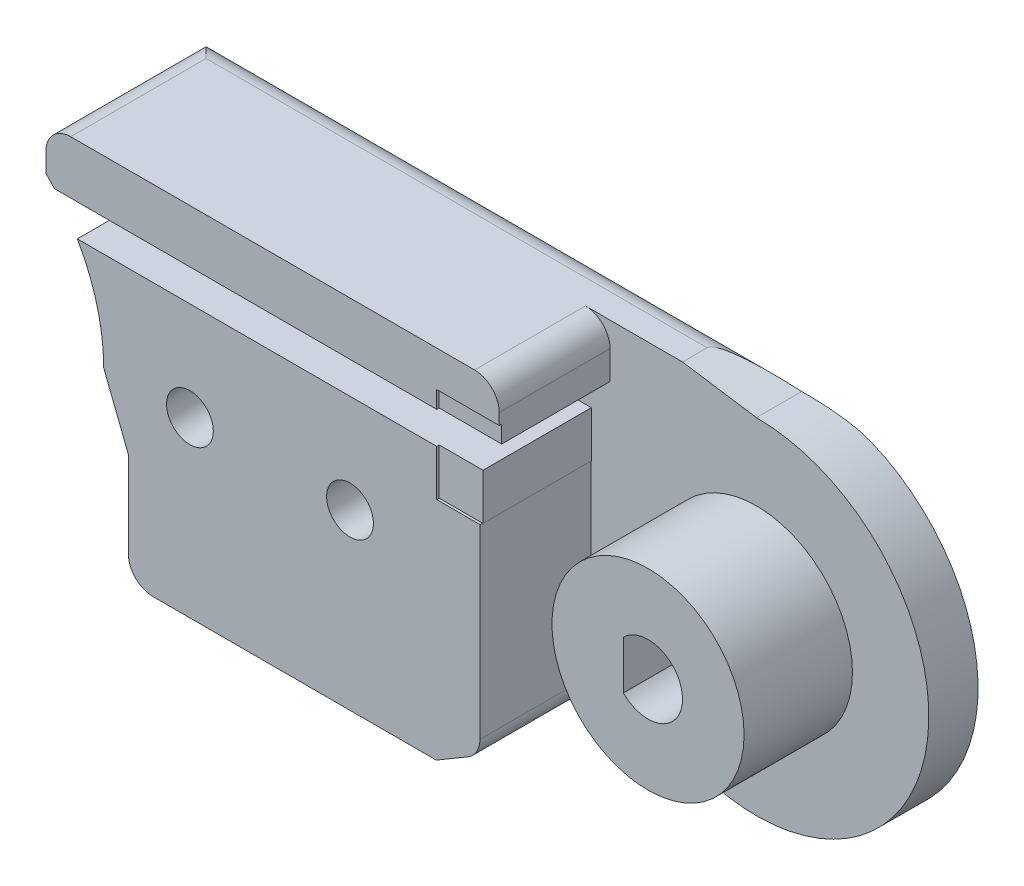
SolidWorks part; units mm, degrees
ref_plane "Front Plane" through (0, 0, 0) normal (0, 0, 1) x (1, 0, 0)
ref_plane "Top Plane" through (0, 0, 0) normal (0, 1, 0) x (1, 0, 0)
ref_plane "Right Plane" through (0, 0, 0) normal (1, 0, 0) x (0, 0, -1)
sketch "Sketch3" plane through (0, 0, 0) normal (0, 0, 1) x (1, 0, 0)
  line L7 (8, 0) -> (9, -2.5431)
  line L11 (30, 7) -> (27, 7.4569)
  line L13 (0, 7) -> (0, 7.5) construction
  line L14 (0, 7.5) -> (-22.3287, 7.5) construction
  line L15 (0, 5.3) -> (-14, 5.3) construction
  line L16 (0, 4) -> (-14, 4) construction
  line L17 (-14, 4) -> (-14, 5.3) construction
  line L18 (5.6569, 5.6569) -> (5.6569, 7.4569)
  line L19 (5.6569, 7.4569) -> (27, 7.4569)
  line L20 (21.5, -7.0431) -> (9, -7.0431)
  line L21 (9, -7.0431) -> (9, -2.5431)
  line L23 (25.0503, -4.9497) -> (21.5, -7.0431)
  arc A4 (8, 0) -> (5.6569, 5.6569) centre (0, 0) ccw
  arc A5 (25.0503, -4.9497) -> (30, 7) centre (30, 0) ccw
  circle A6 centre (0, 0) radius 7 construction
  circle A7 centre (0, 0) radius 3.9 construction
  circle A8 centre (0, 0) radius 5.3 construction
  circle A9 centre (0, 0) radius 4 construction
  dimension "D3" = 3.5503
  dimension "D17" = 14
  dimension "D4" = 14.5
  dimension "D5" = 135
  dimension "D2" = 5.6569
  dimension "D6" = 12.5
  dimension "D7" = 4.5
  dimension "D8" = 1
  dimension "D9" = 45
  dimension "D11" = 1.8
  dimension "D12" = 30
  dimension "D14" = 3
extrude "Boss-Extrude1" add sketch "Sketch3" along normal blind 2 contours A5 L11 L19 L18 A4 L7 L21 L20 L23
sketch "Sketch20" plane through (0, 0, 0) normal (0, 0, 1) x (1, 0, 0)
  line L0 (0, 7) -> (0, 7.5) construction
  line L1 (0, 7.5) -> (-19.4737, 7.5) construction
  line L2 (0, 5.3) -> (-14, 5.3) construction
  line L3 (0, 4) -> (-14, 4) construction
  line L4 (-14, 4) -> (-14, 5.3) construction
  line L5 (0, 5.3) -> (17.4849, 5.3) construction
  line L6 (17.4849, 5.3) -> (17.4849, 4) construction
  line L7 (17.4849, 4) -> (0, 4) construction
  line L8 (-2.5, 7.5) -> (-2.5, 2.868) construction
  circle A0 centre (0, 0) radius 7 construction
  circle A1 centre (0, 0) radius 3.9 construction
  circle A3 centre (0, 0) radius 5.3 construction
  circle A4 centre (0, 0) radius 4 construction
  circle A5 centre (0, 0) radius 2 construction
  dimension "D1" = 0
  dimension "D2" = 2.5
ref_plane "Plane1" through (0, 0, 2) normal (0, 0, 1) x (1, 0, 0)
sketch "Sketch4" plane through (0, 0, 2) normal (0, 0, 1) x (1, 0, 0)
  line L4 (5.6569, 5.6569) -> (5.6569, 7.5)
  line L5 (5.6569, 5.6569) -> (5.6569, 7.4569) construction
  line L6 (5.6569, 7.5) -> (21.5, 7.5)
  line L10 (8, 0) -> (9, -2.5431)
  line L11 (9, -2.5431) -> (9, -7.0431)
  line L12 (9, -7.0431) -> (21.5, -7.0431)
  line L13 (21.5, -7.0431) -> (21.5, 7.5)
  arc A0 (8, 0) -> (5.6569, 5.6569) centre (0, 0) ccw construction
  arc A3 (8, 0) -> (5.6569, 5.6569) centre (0, 0) ccw
sketch "Sketch22" plane through (0, 0, 2) normal (0, 0, 1) x (1, 0, 0)
  line L1 (5.6569, 7.4569) -> (21.5, 7.4569)
  line L6 (8, 0) -> (9, -2.5431)
  line L7 (9, -2.5431) -> (9, -7.0431)
  line L8 (9, -7.0431) -> (21.5, -7.0431)
  line L10 (21.5, 7.4569) -> (27, 7.4569)
  line L11 (27, 7.4569) -> (27, 2.1289)
  line L12 (27, 2.1289) -> (23.2751, 2.1289)
  line L13 (21.5, -7.0431) -> (23.2751, -5.9964)
  line L14 (25.0503, -4.9497) -> (21.5, -7.0431) construction
  line L15 (23.2751, -5.9964) -> (23.2751, 2.1289)
  line L16 (5.6569, 7.4569) -> (5.6569, 5.6569)
  arc A0 (8, 0) -> (5.6569, 5.6569) centre (0, 0) ccw
  dimension "D1" = 5.328
extrude "Boss-Extrude6" add sketch "Sketch22" along normal blind 4.5
sketch "Sketch25" plane through (0, 0, 2) normal (0, 0, 1) x (1, 0, 0)
  line L0 (0, 5.3) -> (18.0981, 5.3) construction
  line L1 (0, 4) -> (18.0981, 4) construction
  line L2 (18.0981, 4) -> (18.0981, 5.3) construction
sketch "Sketch26" plane through (0, 0, 2) normal (0, 0, 1) x (1, 0, 0)
  line L1 (18.0981, 5.3) -> (2.5301, 5.3)
  line L2 (18.0981, 4) -> (2.5301, 4)
  line L3 (2.5301, 5.3) -> (2.5301, 4)
  line L4 (18.0981, 5.3) -> (27, 5.3)
  line L5 (27, 2.1289) -> (27, 7.4569) construction
  line L6 (27, 5.3) -> (27, 4)
  line L7 (27, 4) -> (18.0981, 4)
extrude "Cut-Extrude6" cut sketch "Sketch26" along normal blind 4.5
ref_plane "Plane18" through (0, 0, 6.5) normal (0, 0, 1) x (1, 0, 0)
sketch "Sketch31" plane through (0, 0, 6.5) normal (0, 0, 1) x (1, 0, 0)
  line L0 (2.4327, 5.6569) -> (0, 5.6569)
  line L4 (9, -5.6569) -> (0, -5.6569)
  line L7 (2.4327, 5.6569) -> (5.6569, 5.6569)
  line L8 (5.6569, 5.6569) -> (5.6569, 7.4569)
  line L12 (9, -7.0431) -> (9, -5.6569)
  line L13 (9, -2.5431) -> (9, -7.0431) construction
  line L16 (27, 7.4569) -> (27, 2.1289)
  line L17 (27, 2.1289) -> (23.2751, 2.1289)
  line L18 (23.2751, -5.9964) -> (23.2751, 2.1289)
  line L21 (21.5, -7.0431) -> (23.2751, -5.9964)
  line L22 (5.6569, 7.4569) -> (5.6569, 8.9569)
  line L23 (5.6569, 8.9569) -> (27, 8.9569)
  line L24 (27, 8.9569) -> (27, 7.4569)
  line L25 (9, -7.0431) -> (9, -8.5431)
  line L26 (9, -8.5431) -> (21.5, -8.5431)
  line L27 (21.5, -8.5431) -> (21.5, -7.0431)
  line L28 (27, 7.4569) -> (5.6569, 7.4569) construction
  line L29 (9, -7.0431) -> (21.5, -7.0431) construction
  arc A0 (0, 5.6569) -> (0, -5.6569) centre (0, 0) ccw
  dimension "D1" = 5.6569
  dimension "D2" = 5.6569
  dimension "D3" = 1.5
  dimension "D4" = 1.5
extrude "Boss-Extrude14" add sketch "Sketch31" along normal blind 2.3 separate body
sketch "Sketch32" plane through (0, 0, 8.8) normal (0, 0, 1) x (1, 0, 0)
  circle A0 centre (0, 0) radius 3
  dimension "D1" = 6
extrude "Cut-Extrude7" cut sketch "Sketch32" against normal blind 2.3
sketch "Sketch33" plane through (0, 0, 8.8) normal (0, 0, 1) x (1, 0, 0)
  line L1 (5.6569, 8.9569) -> (5.6569, 6.9569)
  line L4 (9, -7.0431) -> (9, -8.5431)
  line L7 (7, -4.1569) -> (23.2751, -4.1569)
  line L11 (9, -8.5431) -> (21.5, -8.5431)
  line L15 (21.5, -8.5431) -> (21.5, -7.0431)
  line L16 (21.5, -7.0431) -> (9, -7.0431)
  line L17 (5.6569, 8.9569) -> (23, 8.9569)
  line L18 (27, 8.9569) -> (5.6569, 8.9569) construction
  line L21 (23, 6.9569) -> (23, 8.9569)
  line L22 (23.2751, -4.1569) -> (23.2751, -2.1569)
  line L23 (23.2751, -2.1569) -> (7, -2.1569)
  line L25 (23.2751, -5.9964) -> (23.2751, 2.1289) construction
  line L27 (5.6569, 6.9569) -> (23, 6.9569)
  line L28 (19, 2.172) -> (7, 2.172)
  line L30 (7, 4.172) -> (19, 4.172)
  line L33 (19, 2.172) -> (19, 4.172)
  line L34 (27, 2.1289) -> (27, 8.9569) construction
  line L35 (9, -8.5431) -> (21.5, -8.5431) construction
  arc A1 (7, -2.1569) -> (7, -4.1569) centre (7, -3.1569) ccw
  arc A2 (7, 4.172) -> (7, 2.172) centre (7, 3.172) ccw
  dimension "D2" = 2
  dimension "D3" = 2
  dimension "D4" = 0
  dimension "D5" = 2
  dimension "D6" = 4
  dimension "D8" = 4
extrude "Boss-Extrude15" add sketch "Sketch33" along normal blind 1.2
sketch "Sketch34" plane through (0, 0, 2) normal (0, 0, 1) x (1, 0, 0)
  line L0 (30, 5.3) -> (18.0981, 5.3) construction
  line L1 (30, 4) -> (18.0981, 4) construction
  circle A0 centre (30, 0) radius 2 construction
  circle A1 centre (30, 0) radius 5.3 construction
  circle A2 centre (30, 0) radius 4 construction
sketch "Sketch35" plane through (0, 0, 8.8) normal (0, 0, 1) x (1, 0, 0)
  line L0 (27, 2.1289) -> (27, 6)
  line L1 (27, 2.1289) -> (21.5204, 2.1289)
  line L2 (27, 6) -> (21.5204, 6)
  line L3 (21.5204, 2.1289) -> (21.5204, 6)
  line L4 (27, 2.1289) -> (27, 8.9569) construction
  dimension "D1" = 5.4796
extrude "Cut-Extrude8" cut sketch "Sketch35" against normal blind 2.4
sketch "Sketch36" plane through (0, 0, 6.4) normal (0, 0, 1) x (1, 0, 0)
  line L0 (27, 2.1289) -> (27, 4)
  line L1 (27, 2.1289) -> (23.3, 2.1289)
  line L2 (27, 4) -> (23.3, 4)
  line L3 (23.3, 2.1289) -> (23.3, 4)
  line L4 (21.5, -7.0431) -> (21.5, 7.5) construction
  dimension "D1" = 1.8
extrude "Cut-Extrude9" cut sketch "Sketch36" against normal blind 4.4
sketch "Sketch37" plane through (0, 0, 2) normal (0, 0, 1) x (1, 0, 0)
  circle A0 centre (30, 0) radius 3.9
  dimension "D1" = 7.8
extrude "Boss-Extrude16" add sketch "Sketch37" along normal blind 4.4
sketch "Sketch39" plane through (0, 0, 6.4) normal (0, 0, 1) x (1, 0, 0)
  line L0 (29, 0.9798) -> (29, -0.9798)
  arc A0 (29, -0.9798) -> (29, 0.9798) centre (30, 0) ccw
  dimension "D2" = 2.8
  dimension "D1" = 1
extrude "Cut-Extrude10" cut sketch "Sketch39" against normal through all
sketch "Sketch43" plane through (0, 0, 8.8) normal (0, 0, 1) x (1, 0, 0)
  line L2 (0, -5.6569) -> (9, -5.6569) construction
  circle A0 centre (11.5, 0) radius 2.5
  circle A1 centre (18, 0) radius 2.5
  dimension "D1" = 2.5
  dimension "D3" = 5
  dimension "D4" = 6.5
  dimension "D2" = 5.6569
extrude "Boss-Extrude17" add sketch "Sketch43" along normal blind 1.2
sketch "Sketch44" plane through (0, 0, 10) normal (0, 0, 1) x (1, 0, 0)
  circle A0 centre (11.5, 0) radius 0.95
  circle A1 centre (18, 0) radius 0.95
  dimension "D1" = 1.9
  dimension "D2" = 1.9
extrude "Cut-Extrude11" cut sketch "Sketch44" against normal through all
sketch "Sketch45" plane through (0, 0, 0) normal (0, 0, -1) x (-1, 0, 0)
  circle A0 centre (-11.5, 0) radius 2
  circle A1 centre (-18, 0) radius 2
extrude "Cut-Extrude12" cut sketch "Sketch45" against normal blind 4.5
ref_plane "Plane17" through (0, 0, 10) normal (0, 0, 1) x (1, 0, 0)
sketch "Sketch48" plane through (0, 0, 2) normal (0, 0, 1) x (1, 0, 0)
  circle A0 centre (30, 0) radius 6 construction
  dimension "D1" = 12
sketch "Sketch49" plane through (0, 6.9569, 0) normal (0, -1, 0) x (1, 0, 0)
  line L0 (5.6569, 10) -> (23, 10) construction
  line L1 (23, 10) -> (23, 8.8) construction
  circle A0 centre (20, 10) radius 0.75
  dimension "D1" = 3
sketch "Sketch50" plane through (0, 0, 10) normal (0, 0, 1) x (1, 0, 0)
  line L0 (20, 6.9569) -> (27.3935, -5.0795) construction
extrude "Cut-Extrude13" cut sketch "Sketch49" against normal blind 3
sketch "Sketch51" plane through (0, 0, 8.8) normal (0, 0, 1) x (1, 0, 0)
  line L0 (27, 8.9569) -> (24.0587, 8.9569)
  line L1 (27, 8.9569) -> (27, 4.9913)
  line L2 (24.0587, 8.9569) -> (24.0587, 4.9913)
  line L3 (27, 4.9913) -> (24.0587, 4.9913)
  line L5 (27, 8.9569) -> (23, 8.9569) construction
extrude "Cut-Extrude14" cut sketch "Sketch51" against normal blind 6.8
fillet "Fillet1" radius 1.5 2 edges at (14.8578, 8.9569, 6.5) (15.25, -8.5431, 6.5)
fillet "Fillet3" radius 1 6 edges at (23.2751, -5.9964, 4.25) (24.0587, 7.4569, 4.25) (9, -7.0431, 3.25) (5.6569, 7.4569, 3.25) (15.25, -7.0431, 0) (16.3284, 7.4569, 0)
split "Split1" trim tools "Plane18" bodies to split 141 139 resulting bodies 142 143
delete or keep bodies "Body-Delete/Keep 1" type delete bodies bodies 142
